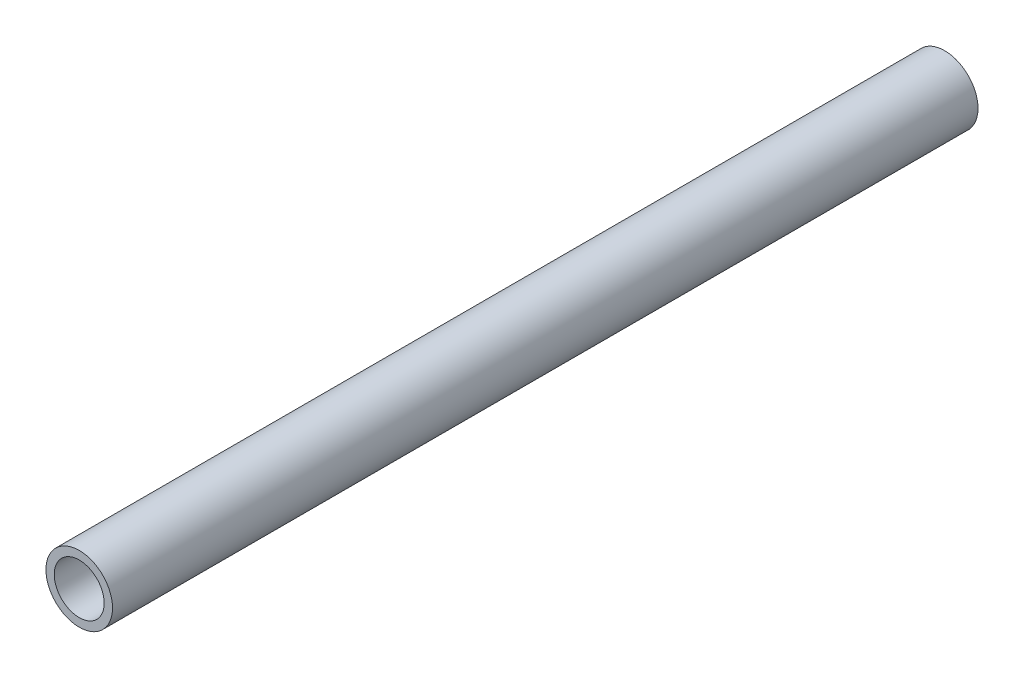
SolidWorks part; units mm, degrees
material "Plain Carbon Steel"
ref_plane "Front" through (0, 0, 0) normal (0, 0, 1) x (1, 0, 0)
ref_plane "Top" through (0, 0, 0) normal (0, 1, 0) x (1, 0, 0)
ref_plane "Right" through (0, 0, 0) normal (1, 0, 0) x (0, 0, -1)
sketch "Sketch2" plane through (0, 0, 0) normal (0, 0, 1) x (1, 0, 0)
  circle A0 centre (0, 0) radius 30
  circle A1 centre (0, 0) radius 40
  dimension "D1" = 80
  dimension "D2" = 60
extrude "Boss-Extrude1" add sketch "Sketch2" along normal blind 1040
